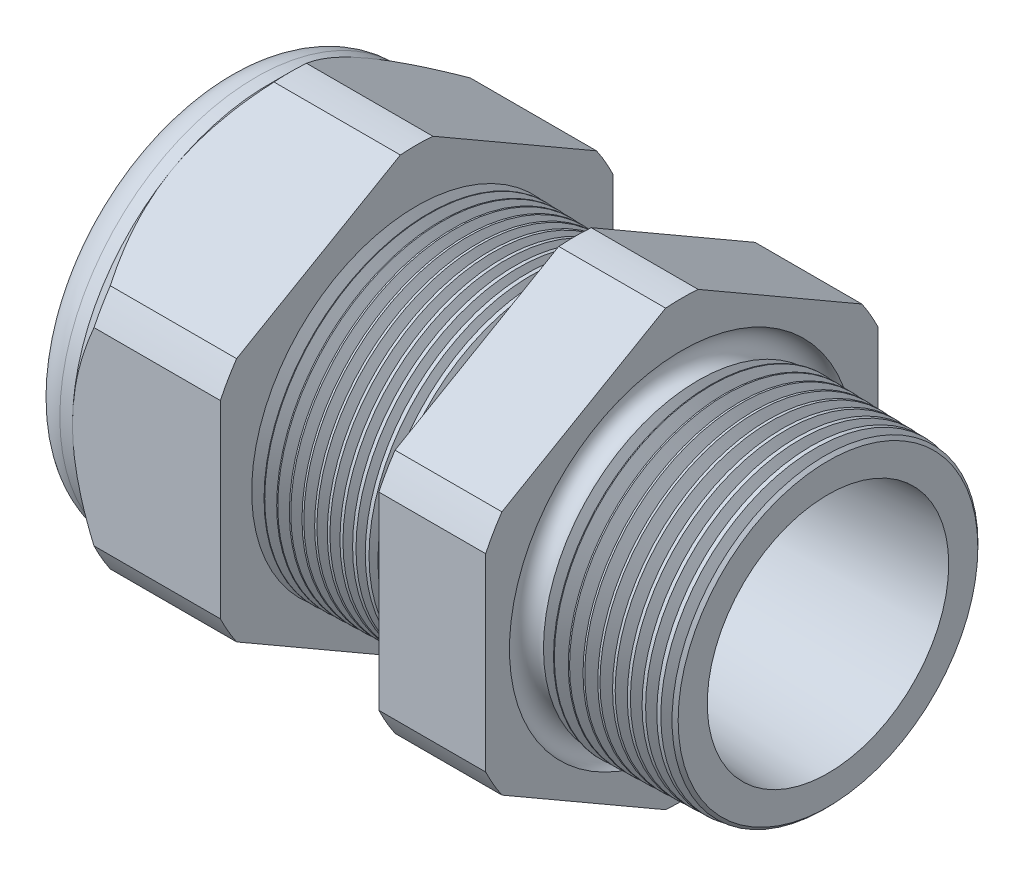
SolidWorks part; units mm, degrees
ref_plane "Front Plane" through (0, 0, 0) normal (0, 0, 1) x (1, 0, 0)
ref_plane "Top Plane" through (0, 0, 0) normal (0, 1, 0) x (1, 0, 0)
ref_plane "Right Plane" through (0, 0, 0) normal (1, 0, 0) x (0, 0, -1)
sketch "Sketch10" plane through (0, 0, 0) normal (0, 0, 1) x (1, 0, 0)
  line L0 (0, 0) -> (-115.3565, 0) construction
  line L1 (-35.814, 5.969) -> (-24.014, 5.969)
  line L2 (1.016, 7.3456) -> (1.016, 9.3776)
  line L3 (-7.874, 9.6104) -> (1.016, 9.3776)
  line L4 (-7.874, 23.876) -> (-7.874, 9.6104)
  line L5 (-7.874, 23.876) -> (-14.374, 23.876)
  line L6 (-14.374, 23.876) -> (-14.374, 9.7806)
  line L7 (-24.014, 10.033) -> (-14.374, 9.7806)
  line L8 (-24.014, 10.033) -> (-24.014, 23.876)
  line L9 (-24.014, 23.876) -> (-33.014, 23.876)
  line L10 (-33.014, 23.876) -> (-33.014, 11.938)
  line L11 (-33.014, 11.938) -> (-35.814, 11.938)
  line L12 (-35.814, 11.938) -> (-35.814, 5.969)
  line L13 (-24.014, 5.969) -> (1.016, 7.3456)
  dimension "D1" = 36.83
  dimension "D2" = 11.938
  dimension "D3" = 1.5
  dimension "D4" = 2.032
  dimension "A" = 20.066
  dimension "D6" = 23.876
  dimension "D8" = 47.752
  dimension "D9" = 2.8
  dimension "D10" = 9
  dimension "D11" = 6.5
  dimension "D" = 8.89
revolve "Revolve2" add sketch "Sketch10" angle 360 about L0
sketch "Sketch12" plane through (-33.014, 0, 0) normal (-1, 0, 0) x (0, 0, 1)
  line L1 (-0.9882, 13.2143) -> (-10.9498, 7.4629)
  line L2 (-11.938, 5.7513) -> (-11.938, -5.7513)
  line L3 (-10.9498, -7.4629) -> (-0.9882, -13.2143)
  line L4 (0.9882, -13.2143) -> (10.9498, -7.4629)
  line L5 (11.938, -5.7513) -> (11.938, 5.7513)
  line L6 (10.9498, 7.4629) -> (0.9882, 13.2143)
  circle A0 centre (0, 0) radius 11.938 construction
  arc A1 (0.9882, 13.2143) -> (-0.9882, 13.2143) centre (0, 0) ccw
  arc A2 (-10.9498, 7.4629) -> (-11.938, 5.7513) centre (0, 0) ccw
  arc A3 (-11.938, -5.7513) -> (-10.9498, -7.4629) centre (0, 0) ccw
  arc A4 (-0.9882, -13.2143) -> (0.9882, -13.2143) centre (0, 0) ccw
  arc A5 (10.9498, -7.4629) -> (11.938, -5.7513) centre (0, 0) ccw
  arc A6 (11.938, 5.7513) -> (10.9498, 7.4629) centre (0, 0) ccw
  dimension "D2" = 26.5024
  dimension "D1" = 23.876
extrude "Cut-Extrude2" cut sketch "Sketch12" against normal through all flip side to cut
fillet "Fillet4" radius 2.032 1 edges at (-35.814, 0, -11.938)
sketch "Sketch19" plane through (-33.014, 0, 0) normal (-1, 0, 0) x (0, 0, 1)
  line L0 (11.938, 0) -> (11.938, 5.7513) construction
  circle A0 centre (0, 0) radius 11.938
extrude "Cut-Extrude3" cut sketch "Sketch19" against normal blind 2 draft 45 flip side to cut
chamfer "Chamfer1" distance 0.254 angle 45 1 edges at (1.016, 0, -9.3776)
sketch "Sketch21" plane through (-35.814, 0, 0) normal (-1, 0, 0) x (0, 0, 1)
  circle A0 centre (0, 0) radius 5.969
  circle A2 centre (0, 0) radius 5.969 construction
extrude "plug" add sketch "Sketch21" against normal blind 6.35 separate body
sketch "Sketch22" plane through (-35.814, 0, 0) normal (-1, 0, 0) x (0, 0, 1)
  circle A0 centre (0, 0) radius 5.715
  circle A1 centre (0, 0) radius 5.969 construction
  dimension "D1" = 0.254
extrude "Cut-Extrude4" cut sketch "Sketch22" against normal blind 0.508
sketch "Sketch27" plane through (-35.306, 0, 0) normal (-1, 0, 0) x (0, 0, 1)
  line L0 (-4.3624, 0) -> (4.3624, 0) construction
  circle A0 centre (-3.1648, 0) radius 2.54
  circle A1 centre (0, 0) radius 5.715 construction
  dimension "D1" = 0.0102
  dimension "holedia" = 5.08
extrude "plugholes" cut sketch "Sketch27" against normal through all
pattern_circular "CirPattern1" count 3 over 360 about axis through (0, 0, 0) along (1, 0, 0) of "plugholes"
sketch "Sketch28" [suppressed] plane through (-29.464, 0, 0) normal (-1, 0, 0) x (0, 0, 1)
  circle A0 centre (0, 0) radius 0.762
  dimension "midholedia" = 5.08
extrude "midhole" [suppressed] cut sketch "Sketch28" against normal through all
sketch "Sketch29" plane through (0, 0, 0) normal (0, 0, 1) x (1, 0, 0)
  line L0 (-24.014, 10.033) -> (-23.281, 10.0138)
  line L1 (-14.374, 9.7806) -> (-24.014, 10.033) construction
  line L2 (-23.281, 10.0138) -> (-23.6641, 9.3886)
  line L3 (-23.6641, 9.3886) -> (-24.014, 10.033)
  dimension "D1" = 60
  dimension "D2" = 60
  dimension "D3" = 0.635
revolve "Cut-Revolve1" cut sketch "Sketch29" angle 360 about axis through (0, 0, 0) along (-1, 0, 0)
pattern_linear "LPattern1" count 13 spacing 0.762 along (1, 0, 0) of "Cut-Revolve1"
sketch "Sketch30" plane through (0, 0, 0) normal (0, 0, 1) x (1, 0, 0)
  line L0 (-7.874, 9.6104) -> (-6.9944, 9.5873)
  line L1 (-7.874, 13.2143) -> (-7.874, 7.4629) construction
  line L2 (0.7621, 9.3842) -> (-7.874, 9.6104) construction
  line L3 (-6.9944, 9.5873) -> (-7.4542, 8.8371)
  line L4 (-7.4542, 8.8371) -> (-7.874, 9.6104)
  dimension "D1" = 60
  dimension "D2" = 60
  dimension "D3" = 0.762
revolve "Cut-Revolve2" cut sketch "Sketch30" angle 360 about axis through (0, 0, 0) along (-1, 0, 0)
pattern_linear "LPattern2" count 10 spacing 0.889 along (1, 0, 0) of "Cut-Revolve2"
sketch "Sketch31" [suppressed] plane through (-38.354, 0, 0) normal (-1, 0, 0) x (0, 0, 1)
  line L0 (-1.905, 1.905) -> (1.905, 1.905)
  line L1 (-1.905, -1.905) -> (1.905, -1.905)
  circle A0 centre (0, 0) radius 1.905 construction
  arc A1 (-1.905, 1.905) -> (-1.905, -1.905) centre (-1.905, 0) ccw
  arc A2 (1.905, 1.905) -> (1.905, -1.905) centre (1.905, 0) cw
extrude "Cut-Extrude5" [suppressed] cut sketch "Sketch31" against normal through all
sketch "Sketch32" plane through (0, 0, 0) normal (0, 0, 1) x (1, 0, 0)
  line L0 (-7.874, 13.2143) -> (-7.874, 7.4629) construction
  circle A0 centre (-7.747, 9.6104) radius 0.889
  dimension "D2" = 1.778
  dimension "D1" = 0.127
revolve "Cut-Revolve3" cut sketch "Sketch32" angle 360 about axis through (0, 0, 0) along (-1, 0, 0)
